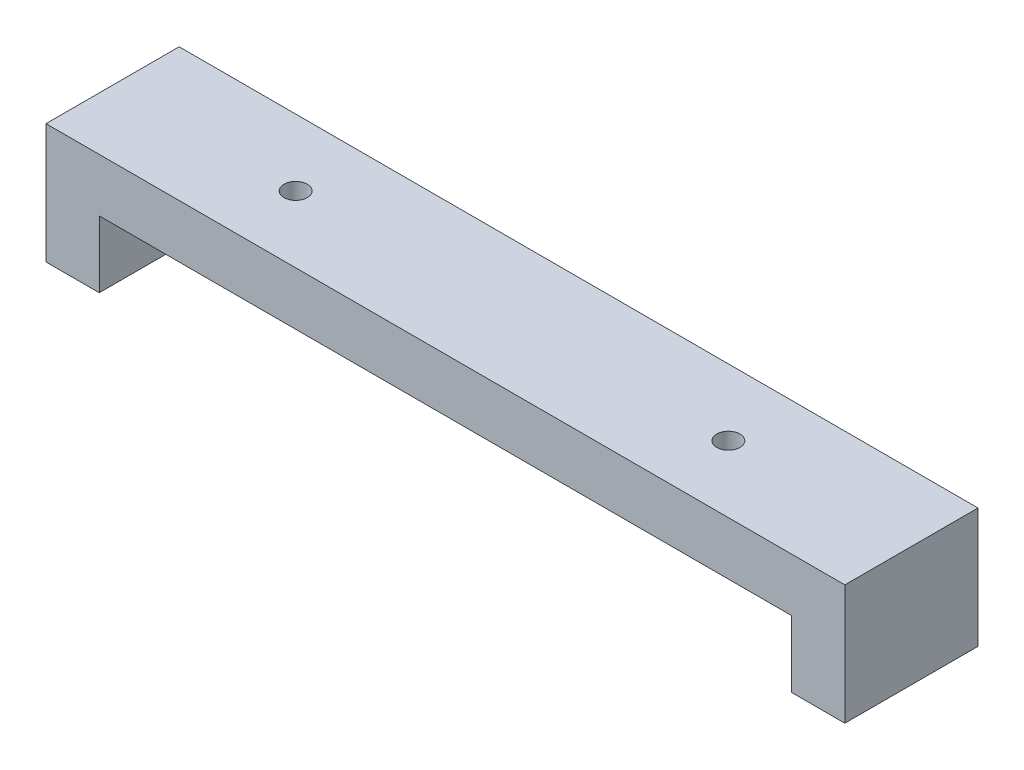
SolidWorks part; units mm, degrees
ref_plane "Front Plane" through (0, 0, 0) normal (0, 0, 1) x (1, 0, 0)
ref_plane "Top Plane" through (0, 0, 0) normal (0, 1, 0) x (1, 0, 0)
ref_plane "Right Plane" through (0, 0, 0) normal (1, 0, 0) x (0, 0, -1)
sketch "Sketch1" plane through (0, 0, 0) normal (0, 1, 0) x (1, 0, 0)
  line L1 (-60, 10) -> (60, 10)
  line L2 (-60, 10) -> (-60, -10)
  line L3 (-60, -10) -> (60, -10)
  line L4 (60, 10) -> (60, -10)
  line L5 (-60, 10) -> (60, -10) construction
  line L6 (-60, -10) -> (60, 10) construction
  point P0 (0, 0)
  dimension "D1" = 120
  dimension "D2" = 20
extrude "Boss-Extrude1" add sketch "Sketch1" along normal blind 8
sketch "Sketch2" plane through (0, 0, 0) normal (0, -1, 0) x (1, 0, 0)
  line L0 (-60, 10) -> (60, 10) construction
  line L1 (60, -10) -> (52, -10)
  line L2 (60, -10) -> (60, 10)
  line L3 (60, 10) -> (52, 10)
  line L4 (52, -10) -> (52, 10)
  line L6 (-60, -10) -> (-52, -10)
  line L7 (-60, -10) -> (-60, 10)
  line L8 (-60, 10) -> (-52, 10)
  line L9 (-52, -10) -> (-52, 10)
  dimension "D1" = 8
  dimension "D2" = 8
extrude "Boss-Extrude2" add sketch "Sketch2" along normal blind 10
sketch "Sketch3" plane through (0, 0, 0) normal (0, -1, 0) x (1, 0, 0)
  line L0 (-52, 0) -> (52, 0) construction
  line L1 (-52, -10) -> (-52, 10) construction
  line L2 (52, 10) -> (52, -10) construction
  circle A0 centre (32.5, 0) radius 1.75
  circle A1 centre (-32.5, 0) radius 1.75
  point P13 (14.9318, -6.024)
  dimension "D3" = 3.5
  dimension "D4" = 3.5
  dimension "D1" = 32.5
  dimension "D2" = 32.5
extrude "Cut-Extrude1" cut sketch "Sketch3" against normal blind 10
